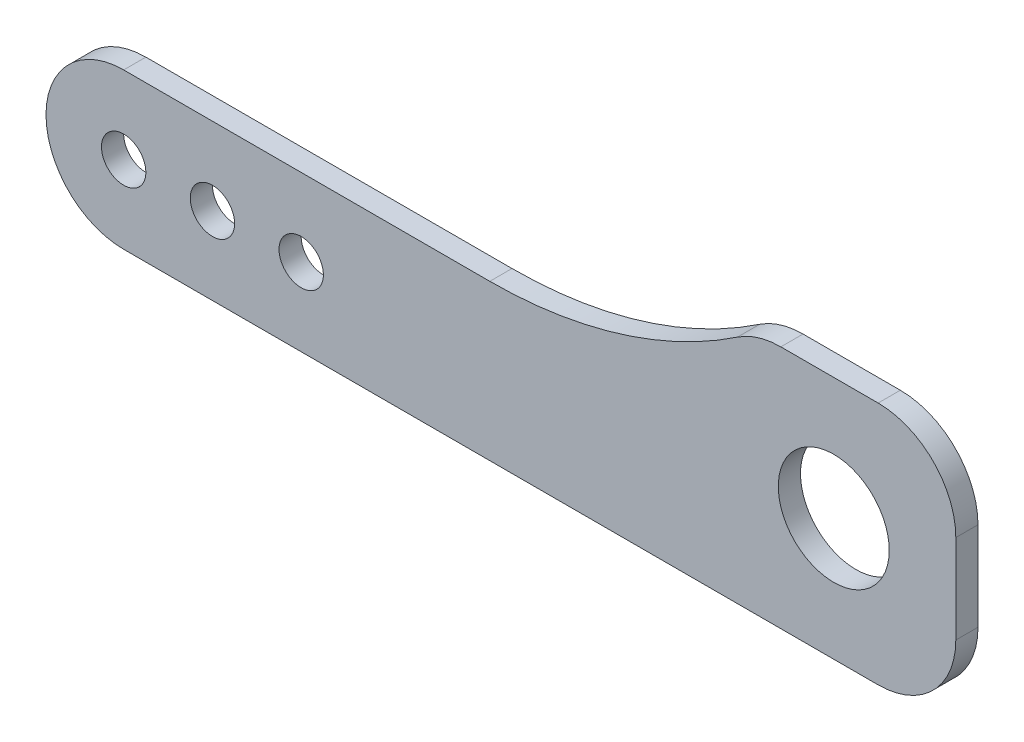
SolidWorks part; units mm, degrees
ref_plane "Front Plane" through (0, 0, 0) normal (0, 0, 1) x (1, 0, 0)
ref_plane "Top Plane" through (0, 0, 0) normal (0, 1, 0) x (1, 0, 0)
ref_plane "Right Plane" through (0, 0, 0) normal (1, 0, 0) x (0, 0, -1)
sketch "Sketch1" plane through (0, 0, 0) normal (0, 0, 1) x (1, 0, 0)
  line L0 (0, 7) -> (33, 7)
  line L1 (68, -7) -> (0, -7)
  line L5 (59.2298, 15) -> (68, 15)
  line L6 (75, 0) -> (75, 8)
  arc A1 (0, -7) -> (0, 7) centre (0, 0) cw
  arc A2 (33, 7) -> (55.3232, 13.8085) centre (33, 47) ccw
  arc A3 (68, -7) -> (75, 0) centre (68, 0) ccw
  arc A4 (68, 15) -> (75, 8) centre (68, 8) cw
  arc A5 (59.2298, 15) -> (55.3232, 13.8085) centre (59.2298, 8) ccw
  point P3 (75, -7)
  point P15 (75, 15)
  point P18 (57, 15)
  dimension "D2" = 7
  dimension "D4" = 40
  dimension "D1" = 7
  dimension "D3" = 22
  dimension "D5" = 18
  dimension "D6" = 75
extrude "Boss-Extrude1" add sketch "Sketch1" along normal blind 2
sketch "Sketch2" plane through (0, 0, 2) normal (0, 0, 1) x (1, 0, 0)
  line L0 (-7, 0) -> (-7, -7) construction
  line L6 (0, 0) -> (8, 0) construction
  line L7 (8, 0) -> (16, 0) construction
  line L8 (-7, -7) -> (0, -7) construction
  circle A0 centre (0, 0) radius 2
  circle A2 centre (8, 0) radius 2
  circle A5 centre (16, 0) radius 2
  arc A6 (0, 7) -> (0, -7) centre (0, 0) ccw construction
  dimension "D1" = 4
  dimension "D2" = 8
extrude "Cut-Extrude1" cut sketch "Sketch2" against normal up to surface (2 mm away) up to face at (47.7635, 5.6039, 0)
sketch "Sketch3" plane through (0, 0, 2) normal (0, 0, 1) x (1, 0, 0)
  line L0 (75, 0) -> (75, 8) construction
  line L2 (64, 4) -> (75, 4) construction
  line L3 (64, 4) -> (64, -7) construction
  line L4 (0, -7) -> (68, -7) construction
  circle A0 centre (64, 4) radius 5
  dimension "D1" = 10
extrude "Cut-Extrude2" cut sketch "Sketch3" against normal up to surface (2 mm away) up to face at (2, 0, 0)
